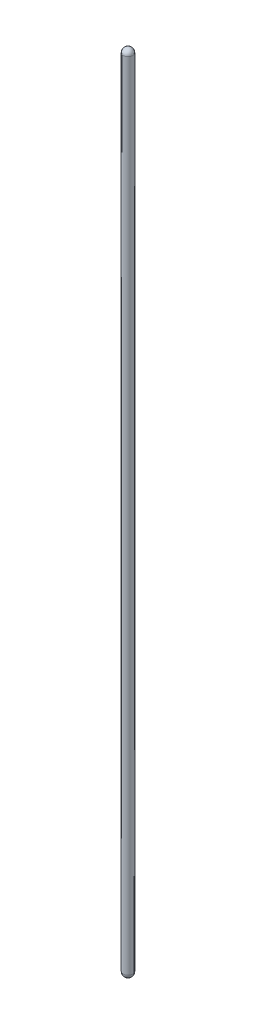
SolidWorks part; units mm, degrees
ref_plane "Ön Düzlem" through (0, 0, 0) normal (0, 0, 1) x (1, 0, 0)
ref_plane "Üst Düzlem" through (0, 0, 0) normal (0, 1, 0) x (1, 0, 0)
ref_plane "Sağ Düzlem" through (0, 0, 0) normal (1, 0, 0) x (0, 0, -1)
sketch "Çizim2" plane through (0, 0, 0) normal (0, 1, 0) x (1, 0, 0)
  circle A0 centre (0, 0) radius 0.5
  dimension "D1" = 1
extrude "Yükseklik-Ekstrüzyon1" add sketch "Çizim2" along normal blind 84
fillet "Radyus1" radius 0.5 1 edges at (0, 84, 0.5)
fillet "Radyus4" radius 0.5 1 edges at (0, 0, 0.5)
